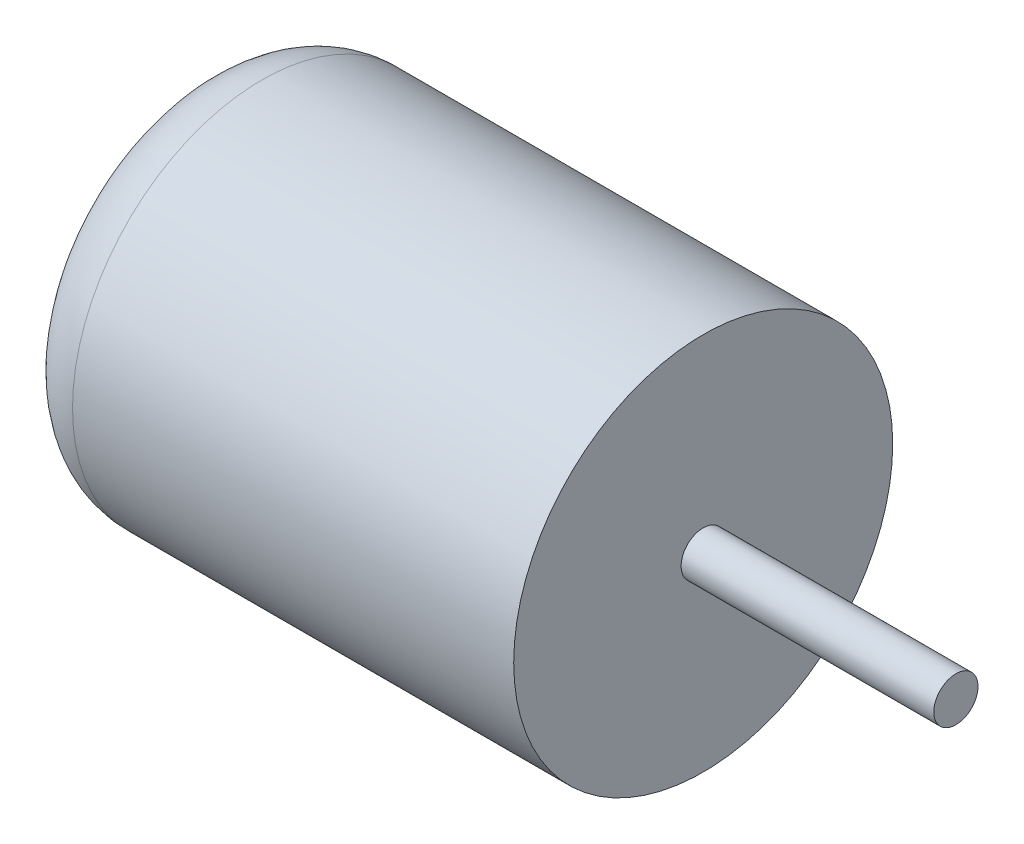
SolidWorks part; units mm, degrees
material "304, 316 OR 302 SSTL"
ref_plane "Front" through (0, 0, 0) normal (0, 0, 1) x (1, 0, 0)
ref_plane "Top" through (0, 0, 0) normal (0, 1, 0) x (1, 0, 0)
ref_plane "Right" through (0, 0, 0) normal (1, 0, 0) x (0, 0, -1)
sketch "Sketch1" plane through (0, 0, 0) normal (1, 0, 0) x (0, 0, -1)
  circle A0 centre (0, 0) radius 7.5
  dimension "D1" = 15
extrude "Boss-Extrude1" add sketch "Sketch1" along normal blind 20
sketch "Sketch2" plane through (20, 0, 0) normal (1, 0, 0) x (0, 0, -1)
  circle A0 centre (0, 0) radius 0.875
  dimension "D1" = 1.75
extrude "Boss-Extrude2" add sketch "Sketch2" along normal blind 10
fillet "Fillet1" radius 2.54 1 edges at (0, 0, -7.5)
